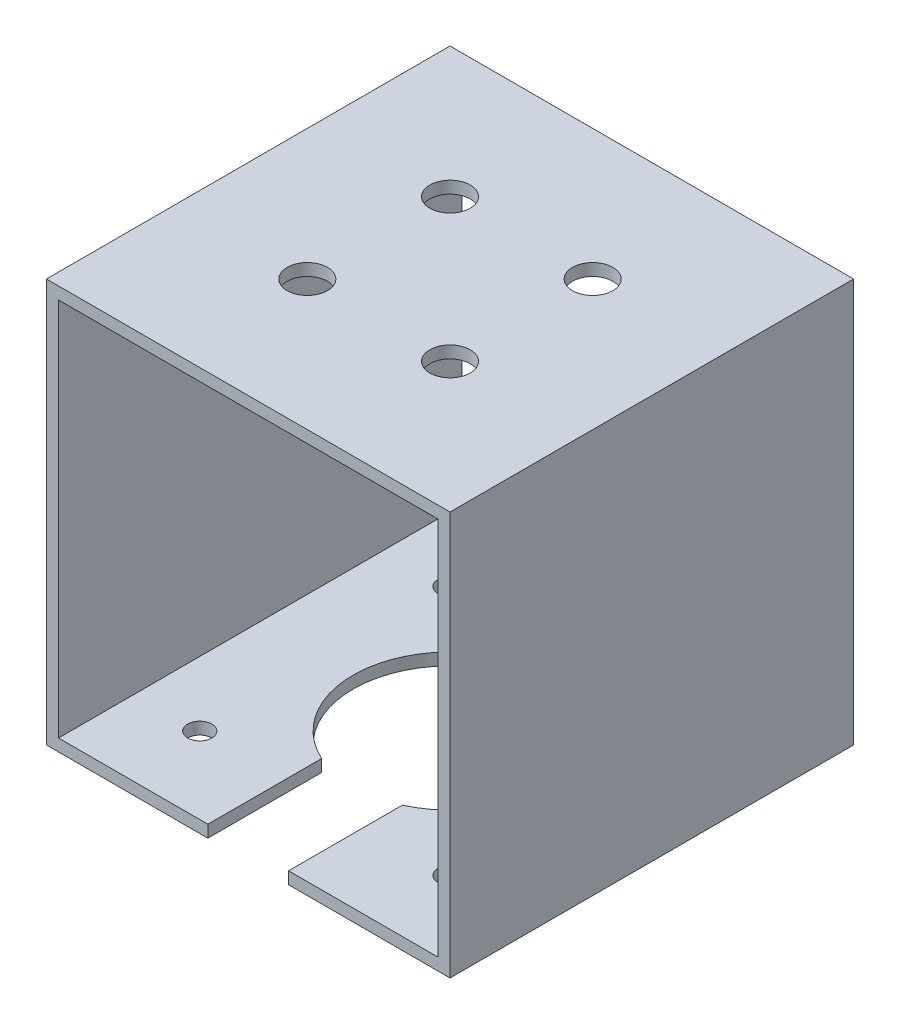
SolidWorks part; units mm, degrees
material "Liga 1060"
ref_plane "Plano frontal" through (0, 0, 0) normal (0, 0, 1) x (1, 0, 0)
ref_plane "Plano superior" through (0, 0, 0) normal (0, 1, 0) x (1, 0, 0)
ref_plane "Plano direito" through (0, 0, 0) normal (1, 0, 0) x (0, 0, -1)
sketch "Esboço1" plane through (0, 0, 0) normal (0, 0, 1) x (1, 0, 0)
  line L0 (25, -25) -> (25, 25)
  line L1 (23.5, -23.5) -> (-23.5, -23.5)
  line L2 (23.5, -23.5) -> (23.5, 23.5)
  line L3 (23.5, 23.5) -> (-23.5, 23.5)
  line L4 (-23.5, -23.5) -> (-23.5, 23.5)
  line L5 (23.5, -23.5) -> (-23.5, 23.5) construction
  line L6 (23.5, 23.5) -> (-23.5, -23.5) construction
  line L7 (25, 25) -> (-25, 25)
  line L8 (-25, -25) -> (-25, 25)
  line L9 (25, -25) -> (-25, -25)
  point P0 (0, 0)
  dimension "D1" = 50
  dimension "D2" = 50
  dimension "D3" = 47
extrude "Ressalto-extrusão1" add sketch "Esboço1" along normal blind 50
sketch "Esboço2" plane through (0, 25, 0) normal (0, 1, 0) x (1, 0, 0)
  line L0 (-25, -25) -> (25, -25) construction
  line L1 (-25, -50) -> (-25, 0) construction
  line L2 (25, -50) -> (25, 0) construction
  line L3 (0, 0) -> (0, -50) construction
  line L4 (25, 0) -> (-25, 0) construction
  line L5 (25, -50) -> (-25, -50) construction
  line L6 (0, -25) -> (17.6777, -7.3223) construction
  circle A0 centre (0, -25) radius 25
  circle A1 centre (8.8388, -16.1612) radius 2.5
  circle A2 centre (-8.8388, -16.1612) radius 2.5
  circle A3 centre (8.8388, -33.8388) radius 2.5
  circle A4 centre (-8.8388, -33.8388) radius 2.5
  dimension "D1" = 50
  dimension "D2" = 5
extrude "Corte-extrusão2" cut sketch "Esboço2" against normal blind 10 contours A2 | A1 | A4 | A3
sketch "Esboço3" plane through (0, -23.5, 0) normal (0, 1, 0) x (1, 0, 0)
  line L0 (0, 0) -> (0, -50) construction
  line L1 (-23.5, 0) -> (23.5, 0) construction
  line L2 (-23.5, -50) -> (23.5, -50) construction
  line L3 (0, -25) -> (23.5, -25) construction
  line L4 (23.5, -50) -> (23.5, 0) construction
  circle A0 centre (0, -25) radius 12
  dimension "D1" = 24
extrude "Corte-extrusão3" cut sketch "Esboço3" against normal blind 10
sketch "Esboço4" plane through (0, -25, 0) normal (0, -1, 0) x (1, 0, 0)
  circle A0 centre (15.5, 40.5) radius 1.5 construction
  circle A1 centre (15.5, 9.5) radius 1.5 construction
  circle A2 centre (-15.5, 40.5) radius 1.5 construction
  circle A3 centre (-15.5, 9.5) radius 1.5 construction
  circle A4 centre (15.5, 40.5) radius 1.5
  circle A5 centre (15.5, 9.5) radius 1.5
  circle A6 centre (-15.5, 40.5) radius 1.5
  circle A7 centre (-15.5, 9.5) radius 1.5
extrude "Corte-extrusão5" cut sketch "Esboço4" against normal blind 10
sketch "Esboço5" plane through (0, -25, 0) normal (0, -1, 0) x (1, 0, 0)
  line L0 (-25, 50) -> (25, 50) construction
  line L1 (-5, 68.4151) -> (5, 68.4151)
  line L2 (-5, 68.4151) -> (-5, 31.5849)
  line L3 (-5, 31.5849) -> (5, 31.5849)
  line L4 (5, 68.4151) -> (5, 31.5849)
  line L5 (-5, 68.4151) -> (5, 31.5849) construction
  line L6 (-5, 31.5849) -> (5, 68.4151) construction
  point P0 (0, 50)
  dimension "D1" = 10
extrude "Corte-extrusão6" cut sketch "Esboço5" against normal blind 10
